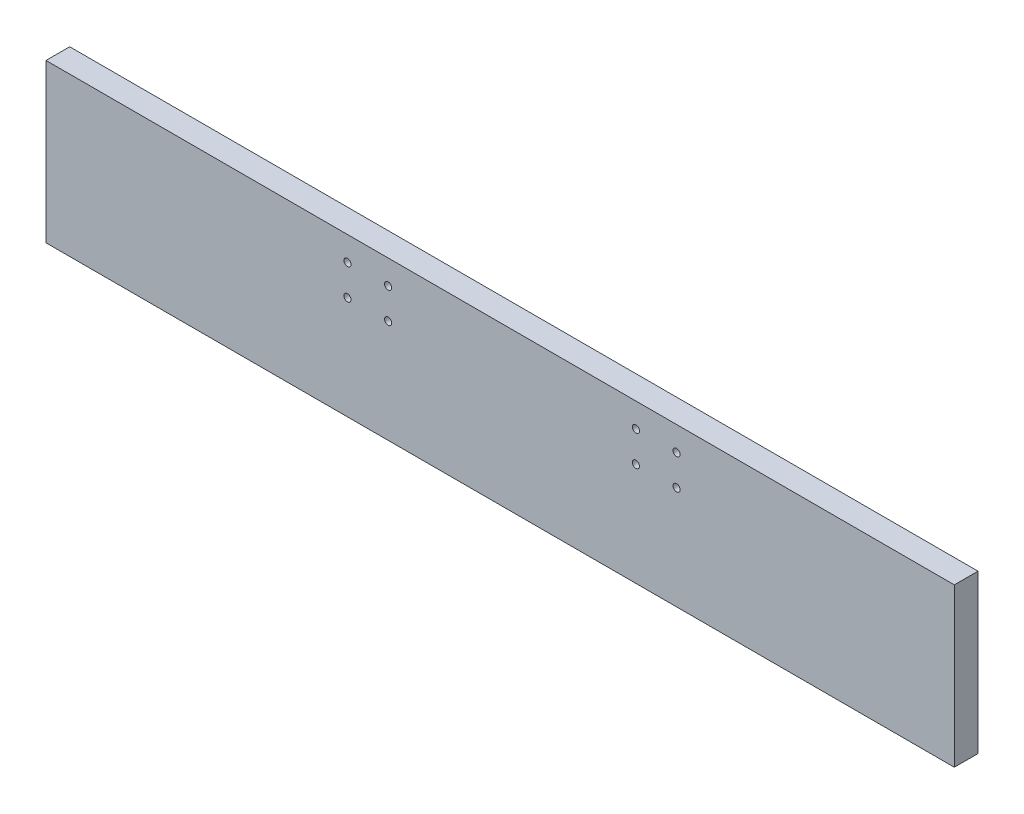
SolidWorks part; units mm, degrees
ref_plane "Front Plane" through (0, 0, 0) normal (0, 0, 1) x (1, 0, 0)
ref_plane "Top Plane" through (0, 0, 0) normal (0, 1, 0) x (1, 0, 0)
ref_plane "Right Plane" through (0, 0, 0) normal (1, 0, 0) x (0, 0, -1)
sketch "Sketch1" plane through (0, 0, 0) normal (0, 0, 1) x (1, 0, 0)
  line L1 (0, 0) -> (730.25, 0)
  line L2 (0, 0) -> (0, 127)
  line L3 (0, 127) -> (730.25, 127)
  line L4 (730.25, 0) -> (730.25, 127)
  dimension "D1" = 730.25
  dimension "D2" = 127
extrude "Boss-Extrude1" add sketch "Sketch1" along normal blind 19.05
sketch "Sketch2" plane through (0, 0, 19.05) normal (0, 0, 1) x (1, 0, 0)
  circle A0 centre (242.3731, 82.9628) radius 2.8512
  circle A1 centre (242.3731, 107.5373) radius 2.8512
  circle A2 centre (275.0248, 107.5373) radius 2.8512
  circle A3 centre (275.0248, 82.9628) radius 2.8511
  circle A4 centre (474.2751, 82.9628) radius 2.8511
  circle A5 centre (474.2751, 107.5373) radius 2.8511
  circle A6 centre (506.9268, 107.5373) radius 2.8512
  circle A7 centre (506.9268, 82.9628) radius 2.8512
extrude "Cut-Extrude1" cut sketch "Sketch2" against normal up to next
